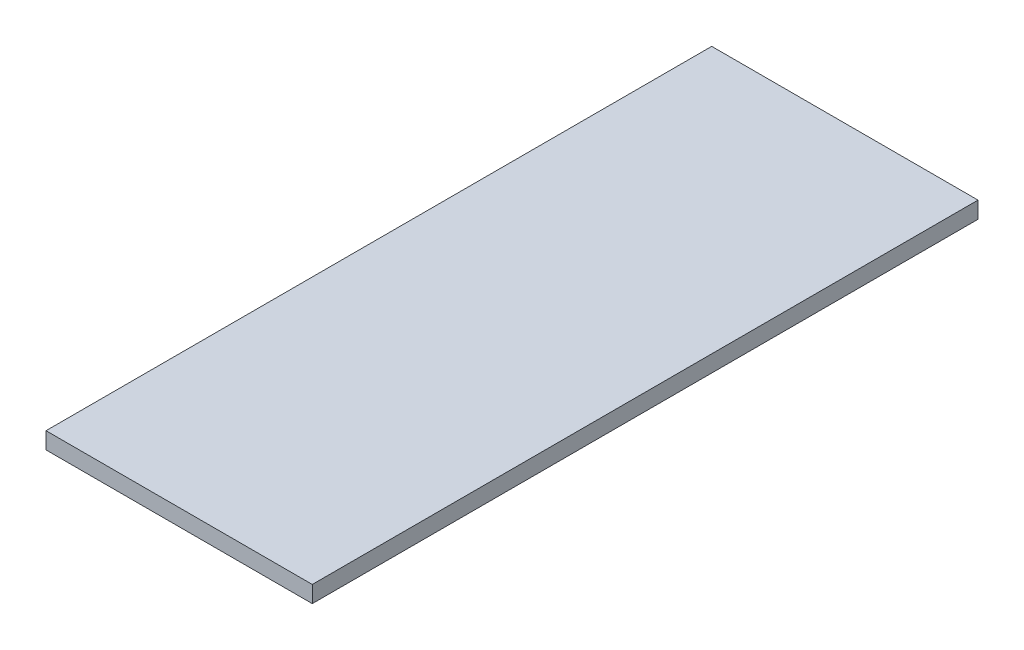
SolidWorks part; units mm, degrees
ref_plane "Front Plane" through (0, 0, 0) normal (0, 0, 1) x (1, 0, 0)
ref_plane "Top Plane" through (0, 0, 0) normal (0, 1, 0) x (1, 0, 0)
ref_plane "Right Plane" through (0, 0, 0) normal (1, 0, 0) x (0, 0, -1)
sketch "Sketch2" plane through (0, 0, 0) normal (0, 1, 0) x (1, 0, 0)
  line L1 (0, 0) -> (-101.6, 0)
  line L2 (0, 0) -> (0, 254)
  line L3 (0, 254) -> (-101.6, 254)
  line L4 (-101.6, 0) -> (-101.6, 254)
  dimension "D1" = 101.6
  dimension "D2" = 254
extrude "Boss-Extrude2" add sketch "Sketch2" along normal blind 6.35
